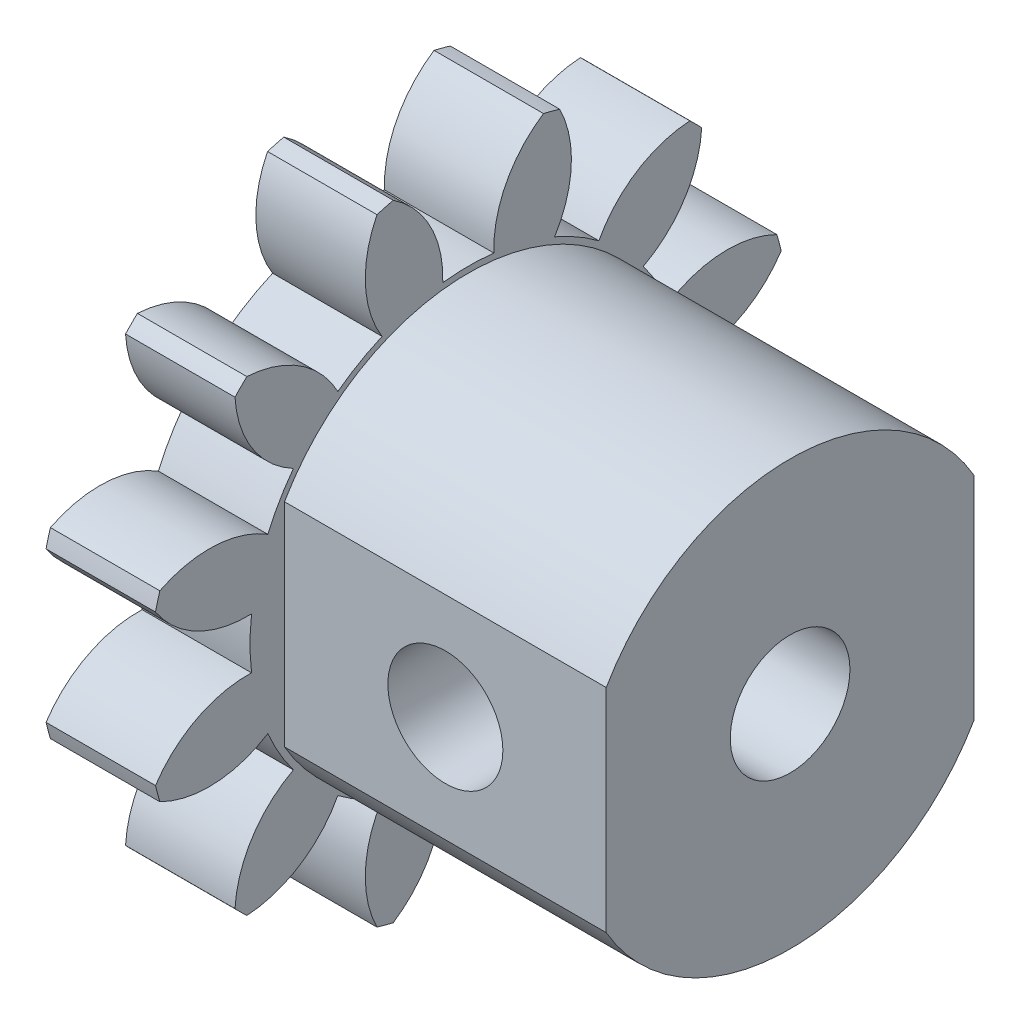
SolidWorks part; units mm, degrees
ref_plane "Plane1" through (0, 0, 0) normal (0, 0, 1) x (1, 0, 0)
ref_plane "Plane2" through (0, 0, 0) normal (0, 1, 0) x (1, 0, 0)
ref_plane "Plane3" through (0, 0, 0) normal (1, 0, 0) x (0, 0, -1)
sketch "HoldingSke" plane through (0, 0, 0) normal (0, 1, 0) x (1, 0, 0)
  line L0 (0, 0) -> (0.4891, -0.104)
  line L1 (-15, 0) -> (100, 0) construction
  line L2 (0, 0) -> (-2.1039, 2.3779)
  line L3 (0, 0) -> (-11.863, 4.5341)
  line L4 (0, 0) -> (8.4473, 1.7955)
  line L5 (0, 0) -> (-46.8476, -17.4728)
  line L6 (0, 0) -> (-3.9479, -2.6637)
  line L7 (-2.1039, 2.3779) -> (8.6586, 51.2059)
  line L8 (-76.2, 54.61) -> (-74.4, 54.61)
  line L9 (-71.009, 38.7566) -> (-53.1078, 45.2721)
  line L10 (-76.2, 71.12) -> (104.1128, 71.12)
  line L11 (0, 0) -> (-4.7625, 0)
  line L12 (-76.2, 101.6) -> (-76.133, 101.6)
  line L13 (24.9733, 27.94) -> (52.9518, 28.4284)
  line L14 (24.9733, 27.94) -> (24.9743, 27.94)
  line L15 (24.9733, 27.94) -> (100.4006, 29.5858)
  line L16 (-63.627, -2) -> (-12.827, -2)
  circle A0 centre (0, 0) radius 5
  circle A1 centre (0, 0) radius 9.499
  circle A2 centre (0, 0) radius 37.5
  circle A3 centre (0, 0) radius 5
  dimension "MHD" = 18.998
  dimension "Hub_dia" = 75
  dimension "Bore" = 10
  dimension "MBD" = 10
  dimension "Num_teeth" = 12
  dimension "Pitch_radius" = 180.3128
  dimension "Pitch" = 0.5
  dimension "Width" = 4.7625
  dimension "Overall_len" = 50
  dimension "Show_teeth" = 12
  dimension "Thickness" = 4.7625
  dimension "OAL" = 50.0001
  dimension "T_dim" = 1.8
  dimension "Ap" = 20
  dimension "H" = 19.05
  dimension "Backlash" = 0.067
  dimension "Addendum_fac" = 1
  dimension "Dedendum_fac" = 1.25
  dimension "Clearance_fac" = 0.25
  dimension "Dedendum_add" = 0.001
  dimension "Module" = 2
sketch "BasProSke" plane through (0, 0, 0) normal (0, 1, 0) x (1, 0, 0)
  line L0 (-10, 0) -> (60, 0) construction
  line L1 (0, 0) -> (0, 14)
  line L2 (0, 0) -> (4.7625, 0)
  line L3 (4.7625, 0) -> (4.7625, 14)
  line L4 (4.7625, 14) -> (0, 14)
  dimension "Diameter" = 28
  dimension "Thickness" = 4.7625
revolve "Base-Revolve" add sketch "BasProSke" angle 360 about L0
sketch "TooCutSke" plane through (0, 0, 0) normal (1, 0, 0) x (0, 0, -1)
  line L1 (0, 0) -> (0, 107) construction
  line L2 (0, 0) -> (-1.6834, 11.8813) construction
  line L3 (0, 0) -> (-6.1662, 23.0126) construction
  line L4 (-1.6834, 11.8813) -> (-3.0831, 11.5063) construction
  arc A0 (1.1119, 9.4337) -> (-1.1119, 9.4337) centre (0, 0) ccw
  arc A1 (3.2981, 13.6321) -> (-3.2981, 13.6321) centre (0, 0) ccw
  circle A2 centre (0, 0) radius 12 construction
  circle A3 centre (0, 0) radius 11.2763 construction
  arc A4 (-1.1119, 9.4337) -> (-3.2981, 13.6321) centre (-5.9089, 9.6042) ccw
  arc A5 (3.2981, 13.6321) -> (1.1119, 9.4337) centre (5.9089, 9.6042) ccw
  dimension "Root_dia" = 18.998
  dimension "Overcut_dia" = 28.0508
  dimension "Pitch_dia" = 24
  dimension "Base_dia" = 22.5526
  dimension "Flank_rad" = 4.8
  dimension "Half_ang" = 15
  dimension "Half_CT" = 1.4491
extrude "ToothCut" cut sketch "TooCutSke" along normal through all
fillet "Breaks" [suppressed] radius 0.04
fillet "RootFillets" [suppressed] radius 0.501
pattern_circular "TeethCuts" count 12 every 30 about axis through (-10, 0, 0) along (1, 0, 0) of "ToothCut", "RootFillets", "Breaks"
sketch "HubNeaOneSke" plane through (0, 0, 0) normal (-1, 0, 0) x (0, 0, 1)
  circle A0 centre (0, 0) radius 9.499
  dimension "Diameter" = 18.998
extrude "HubNearOne" [suppressed] add sketch "HubNeaOneSke" along normal blind 45.2376
sketch "HubNeaBotSke" plane through (0, 0, 0) normal (-1, 0, 0) x (0, 0, 1)
  circle A0 centre (0, 0) radius 9.499
  dimension "Diameter" = 18.998
extrude "HubNearBoth" [suppressed] add sketch "HubNeaBotSke" along normal blind 22.6188
ref_plane "FarPln" through (4.7625, 0, 0) normal (1, 0, 0) x (0, 0, -1)
sketch "HubFarSke" plane through (4.7625, 0, 0) normal (1, 0, 0) x (0, 0, -1)
  circle A0 centre (0, 0) radius 9.499
  dimension "Diameter" = 18.998
extrude "HubFar" [suppressed] add sketch "HubFarSke" along normal blind 22.6188
sketch "BorSke" plane through (0, 0, 0) normal (1, 0, 0) x (0, 0, -1)
  circle A0 centre (0, 0) radius 2.6035
  dimension "Diameter" = 5.207
extrude "Bore" cut sketch "BorSke" along normal mid plane 100.0001
sketch "KeySke" plane through (0, 0, 0) normal (1, 0, 0) x (0, 0, -1)
  line L0 (-2, 0) -> (-2, 6.8)
  line L1 (-2, 6.8) -> (2, 6.8)
  line L2 (2, 6.8) -> (2, 0)
  line L3 (0, 0) -> (0, 34) construction
  line L4 (-2, 0) -> (2, 0)
  dimension "Offset" = 6.8
  dimension "Width" = 4
extrude "Keyway" [suppressed] cut sketch "KeySke" along normal mid plane 100.0001
pattern_circular "Keyway2" [suppressed] count 2 every 90 about axis through (-10, 0, 0) along (1, 0, 0)
sketch "Sketch1" plane through (4.7625, 0, 0) normal (1, 0, 0) x (0, 0, -1)
  line L0 (0, 0) -> (14.605, 0) construction
  line L2 (-8, 4.6188) -> (-8, -4.6188)
  line L5 (8, -4.6188) -> (8, 4.6188)
  line L8 (0, -9.2376) -> (4, -6.9282) [skipped]
  line L9 (-8, -4.6188) -> (-4, -6.9282) [skipped]
  line L10 (4, 6.9282) -> (0, 9.2376) [skipped]
  line L11 (-4, 6.9282) -> (-8, 4.6188) [skipped]
  circle A0 centre (0, 0) radius 8 construction
  arc A1 (-8, 4.6188) -> (8, 4.6188) centre (0, 0) cw
  arc A4 (-8, -4.6188) -> (8, -4.6188) centre (0, 0) ccw
extrude "Boss-Extrude1" add sketch "Sketch1" along normal blind 14
sketch "Sketch2" plane through (18.7625, 0, 0) normal (1, 0, 0) x (0, 0, -1)
  circle A0 centre (0, 0) radius 2.6035 construction
  circle A1 centre (0, 0) radius 2.6035
extrude "Cut-Extrude1" cut sketch "Sketch2" against normal through all
sketch "Sketch3" plane through (0, 0, 8) normal (0, 0, 1) x (1, 0, 0)
  line L0 (18.7625, 0) -> (4.7625, 0) construction
  line L3 (18.7625, 4.6188) -> (18.7625, -4.6188) construction
  line L4 (4.7625, -1.1119) -> (4.7625, 1.1119) construction
  circle A0 centre (11.7625, 0) radius 2.5019
  dimension "D1" = 5.0038
extrude "Cut-Extrude2" cut sketch "Sketch3" against normal through all
equation "' \"Module@HoldingSke\" = 6.35"
equation "' \"Num_teeth@HoldingSke\" = 12"
equation "' \"Ap@HoldingSke\" =  20"
equation "' \"Width@HoldingSke\" = 0.5 * 25.4"
equation "' \"Hub_dia@HoldingSke\"= 1 * 25.4"
equation "' \"Overall_len@HoldingSke\" = 1.0 * 25.4"
equation "' \"Bore@HoldingSke\" = 0.75 * 25.4"
equation "' \"T_dim@HoldingSke\" = 0.1 * 25.4"
equation "' \"Width@KeySke\" = 0.25 * 25.4"
equation "' \"Show_teeth@HoldingSke\" = 13"
equation "' \"Backlash@HoldingSke\" = 0.009 * 25.4"
equation "' \"Addendum_fac@HoldingSke\" = 1.0"
equation "' \"Dedendum_fac@HoldingSke\" = 1.25"
equation "' \"Dedendum_add@HoldingSke\" = 0.00005 * 25.4"
equation "' \"Clearance_fac@HoldingSke\" = 0.25"
equation "\"Pitch@HoldingSke\" = 1 / \"Module@HoldingSke\""
equation "\"Overcut_dia@TooCutSke\" = (\"Num_teeth@HoldingSke\" + 2 * \"Addendum_fac@HoldingSke\") / \"Pitch@HoldingSke\" + 0.002 * 25.4"
equation "\"Pitch_dia@TooCutSke\" = \"Num_teeth@HoldingSke\" / \"Pitch@HoldingSke\""
equation "\"Base_dia@TooCutSke\" = \"Num_teeth@HoldingSke\" / \"Pitch@HoldingSke\" * cos((\"Ap@HoldingSke\"  * 3.14159265 / 180))"
equation "\"Root_dia@TooCutSke\" = (\"Num_teeth@HoldingSke\" + 2) / \"Pitch@HoldingSke\" - 2 * (\"Addendum_fac@HoldingSke\" + \"Dedendum_fac@HoldingSke\") / \"Pitch@HoldingSke\" - \"Dedendum_add@HoldingSke\" * 2"
equation "\"Half_ang@TooCutSke\" = 180 / \"Num_teeth@HoldingSke\""
equation "\"Half_CT@TooCutSke\" = \"Num_teeth@HoldingSke\" / \"Pitch@HoldingSke\" * sin((3.14159265 / 2 / \"Num_teeth@HoldingSke\")) / 2 - 7 * \"Backlash@HoldingSke\" / 4"
equation "\"Flank_rad@TooCutSke\" = \"Num_teeth@HoldingSke\" / \"Pitch@HoldingSke\" / 5"
equation "\"Radius@RootFillets\" = \"Clearance_fac@HoldingSke\" / \"Pitch@HoldingSke\" + \"Dedendum_add@HoldingSke\""
equation "\"Break_rad@Breaks\" = 0.02 / \"Pitch@HoldingSke\""
equation "\"Thickness@HoldingSke\" = \"Width@HoldingSke\""
equation "\"OAL@HoldingSke\" = \"Thickness@HoldingSke\""
equation "\"MHD@HoldingSke\" = (\"Num_teeth@HoldingSke\" + 2) / \"Pitch@HoldingSke\" - 2 * (\"Addendum_fac@HoldingSke\" + \"Dedendum_fac@HoldingSke\")  / \"Pitch@HoldingSke\" - \"Dedendum_add@HoldingSke\" * 2"
equation "\"MBD@HoldingSke\" = (\"Num_teeth@HoldingSke\" + 2) / \"Pitch@HoldingSke\" - 2 * (\"Addendum_fac@HoldingSke\" + \"Dedendum_fac@HoldingSke\")  / \"Pitch@HoldingSke\" - \"Dedendum_add@HoldingSke\" * 2 - 0.002 * 25.4"
equation "\"MHD@HoldingSke\" = ((sgn( \"MHD@HoldingSke\" - \"Hub_dia@HoldingSke\" )-1)*( \"MHD@HoldingSke\" - \"Hub_dia@HoldingSke\" ))/-2+ \"Hub_dia@HoldingSke\""
equation "\"MBD@HoldingSke\" = ((sgn( \"MBD@HoldingSke\" - \"Bore@HoldingSke\" )-1)*( \"MBD@HoldingSke\" - \"Bore@HoldingSke\" ))/-2+ \"Bore@HoldingSke\""
equation "\"OAL@HoldingSke\" = ((sgn( \"OAL@HoldingSke\" - \"Overall_len@HoldingSke\" )+1)*( \"OAL@HoldingSke\" - \"Overall_len@HoldingSke\" ))/2 + \"Overall_len@HoldingSke\" + 0.000002 * 25.4"
equation "\"Num_teeth@TeethCuts\" = int( \"Show_teeth@HoldingSke\" ) + 1"
equation "\"Num_teeth@TeethCuts\" = ((sgn( \"Num_teeth@TeethCuts\" - \"Num_teeth@HoldingSke\" )-1)*( \"Num_teeth@TeethCuts\" - \"Num_teeth@HoldingSke\" ))/-2+ \"Num_teeth@HoldingSke\""
equation "\"Num_teeth@TeethCuts\" = ((sgn( \"Num_teeth@TeethCuts\" - 2.0)+1)*( \"Num_teeth@TeethCuts\" - 2.0))/2 +2.0"
equation "\"Angle@TeethCuts\" = 360.0 / \"Num_teeth@HoldingSke\""
equation "\"Diameter@BasProSke\" = (\"Num_teeth@HoldingSke\" + 2 * \"Addendum_fac@HoldingSke\") / \"Pitch@HoldingSke\""
equation "\"Thickness@BasProSke\"  = \"Thickness@HoldingSke\""
equation "' \"Fillet_rad@BasProSke\" =  \"Thickness@HoldingSke\" * 0.05"
equation "\"MHD@HoldingSke\" = ((sgn( \"MHD@HoldingSke\" - \"Root_dia@TooCutSke\" )-1)*( \"MHD@HoldingSke\" - \"Root_dia@TooCutSke\" ))/-2+ \"Root_dia@TooCutSke\""
equation "\"Diameter@HubNeaOneSke\" = \"MHD@HoldingSke\""
equation "\"Length@HubNearOne\" = \"OAL@HoldingSke\" - \"Thickness@BasProSke\""
equation "\"Diameter@HubNeaBotSke\" = \"MHD@HoldingSke\""
equation "\"Length@HubNearBoth\" = ( \"OAL@HoldingSke\" - \"Thickness@BasProSke\" ) / 2.0"
equation "\"Thickness@FarPln\" = \"Thickness@BasProSke\""
equation "\"Diameter@HubFarSke\" = \"MHD@HoldingSke\""
equation "\"Length@HubFar\" = ( \"OAL@HoldingSke\" - \"Thickness@BasProSke\" ) / 2.0"
equation "\"D1@Bore\" = \"OAL@HoldingSke\" * 2.0"
equation "\"D1@Keyway\" = \"OAL@HoldingSke\" * 2.0"
equation "\"Offset@KeySke\" = \"T_dim@HoldingSke\" + \"MBD@HoldingSke\" / 2.0"
